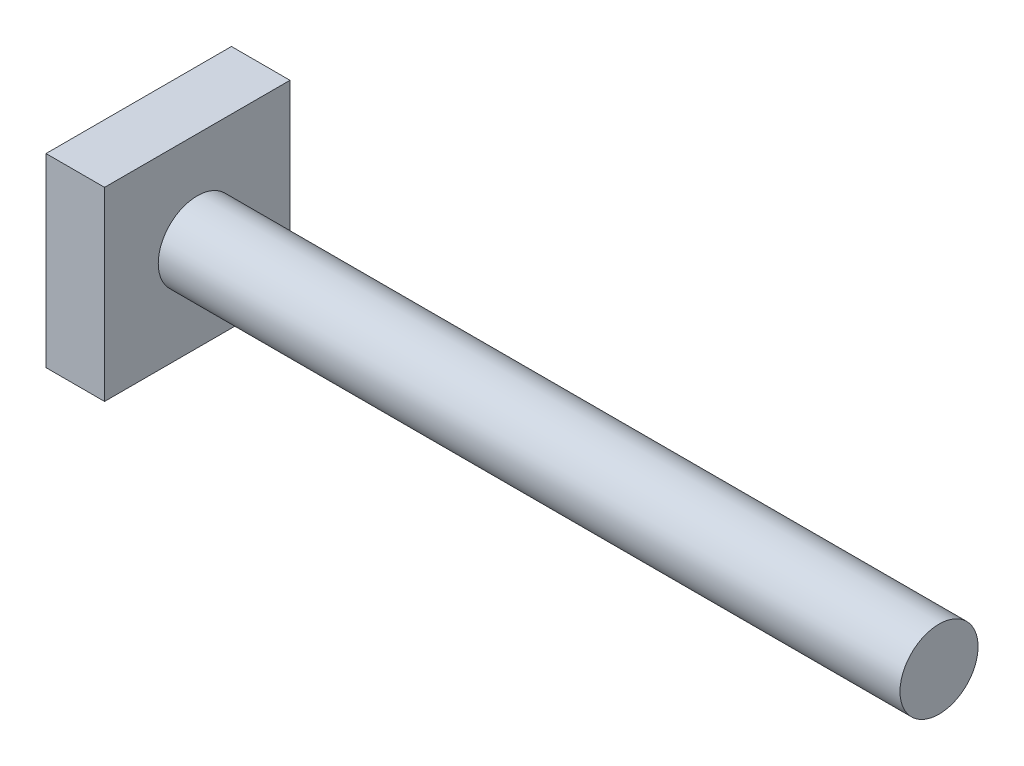
SolidWorks part; units mm, degrees
ref_plane "Front Plane" through (0, 0, 0) normal (0, 0, 1) x (1, 0, 0)
ref_plane "Top Plane" through (0, 0, 0) normal (0, 1, 0) x (1, 0, 0)
ref_plane "Right Plane" through (0, 0, 0) normal (1, 0, 0) x (0, 0, -1)
sketch "Sketch1" plane through (0, 0, 0) normal (0, 0, 1) x (1, 0, 0)
  line L0 (0, 0) -> (76, 0) construction
  line L1 (76, 0) -> (76, 4)
  line L2 (76, 4) -> (0, 4)
  line L3 (0, 4) -> (0, 0)
  line L4 (0, 0) -> (76, 0)
  dimension "D1" = 76
  dimension "D2" = 8
revolve "Revolve1" add sketch "Sketch1" angle 360 about L0
sketch "Sketch2" plane through (0, 0, 0) normal (-1, 0, 0) x (0, 0, 1)
  line L1 (-9.5, 9.5) -> (9.5, 9.5)
  line L2 (-9.5, 9.5) -> (-9.5, -9.5)
  line L3 (-9.5, -9.5) -> (9.5, -9.5)
  line L4 (9.5, 9.5) -> (9.5, -9.5)
  line L5 (-9.5, 9.5) -> (9.5, -9.5) construction
  line L6 (-9.5, -9.5) -> (9.5, 9.5) construction
  point P0 (0, 0)
  dimension "D1" = 19
  dimension "D2" = 19
extrude "Boss-Extrude1" add sketch "Sketch2" along normal blind 6
